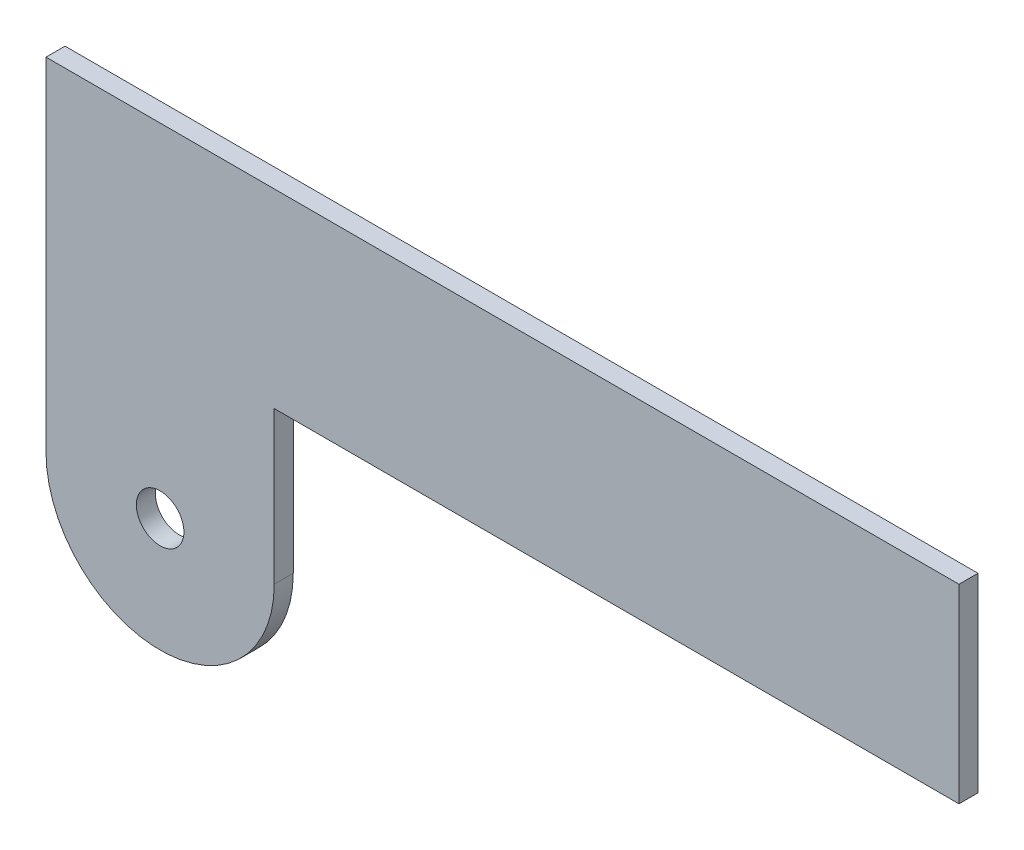
SolidWorks part; units mm, degrees
material "Plain Carbon Steel"
ref_plane "Front Plane" through (0, 0, 0) normal (0, 0, 1) x (1, 0, 0)
ref_plane "Top Plane" through (0, 0, 0) normal (0, 1, 0) x (1, 0, 0)
ref_plane "Right Plane" through (0, 0, 0) normal (1, 0, 0) x (0, 0, -1)
sketch "Sketch1" plane through (0, 0, 0) normal (0, 0, 1) x (1, 0, 0)
  line L0 (152.4, 0) -> (0, 0)
  line L1 (1.7463, 0) -> (-1.7463, 0) construction
  line L2 (0, 0) -> (0, -57.15)
  line L3 (0, -1.7463) -> (0, 1.7463) construction
  line L4 (38.1, -57.15) -> (38.1, -31.75)
  line L5 (38.1, -31.75) -> (152.4, -31.75)
  line L6 (152.4, -31.75) -> (152.4, 0)
  line L7 (152.4, 0) -> (152.4, 0.4446)
  arc A0 (0, -57.15) -> (38.1, -57.15) centre (19.05, -57.15) ccw
  circle A1 centre (19.05, -57.15) radius 3.9688
  dimension "D4" = 19.05
  dimension "D5" = 7.9375
  dimension "D1" = 31.75
  dimension "D2" = 152.4
  dimension "D3" = 25.4
extrude "Boss-Extrude1" add sketch "Sketch1" along normal mid plane 3.175 contours L2 A0 L4 L5 L6 L0 A1
